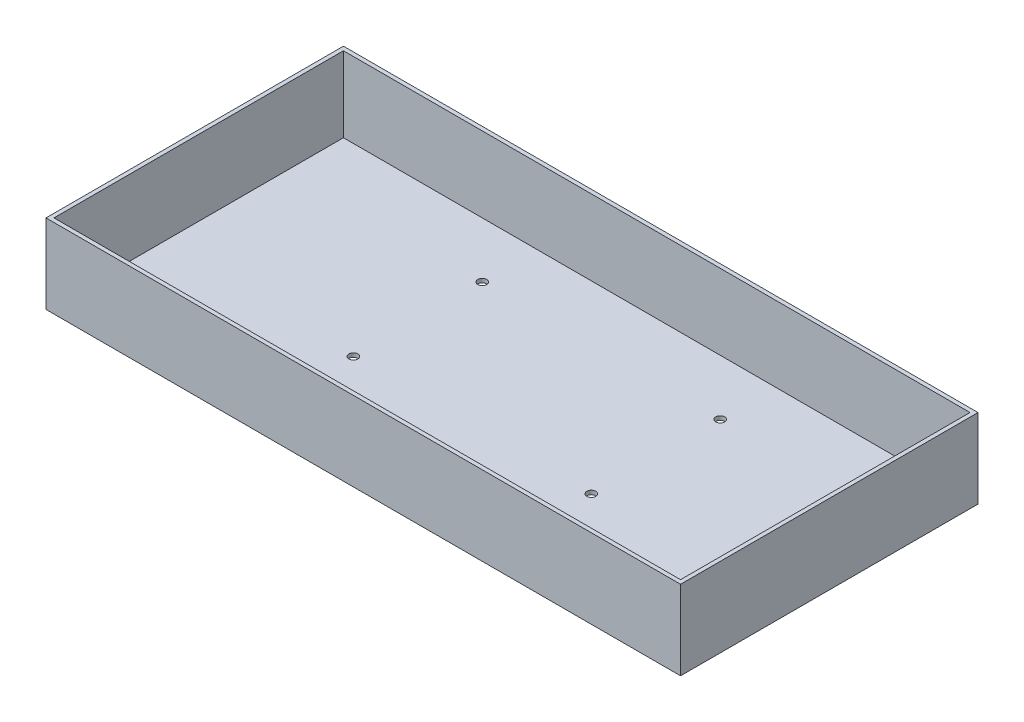
SolidWorks part; units mm, degrees
ref_plane "前视基准面" through (0, 0, 0) normal (0, 0, 1) x (1, 0, 0)
ref_plane "上视基准面" through (0, 0, 0) normal (0, 1, 0) x (1, 0, 0)
ref_plane "右视基准面" through (0, 0, 0) normal (1, 0, 0) x (0, 0, -1)
sketch "草图1" plane through (0, 0, 0) normal (0, 1, 0) x (1, 0, 0)
  line L1 (0, 0) -> (320, 0)
  line L2 (0, 0) -> (0, 150)
  line L3 (0, 150) -> (320, 150)
  line L4 (320, 0) -> (320, 150)
  dimension "D1" = 320
  dimension "D2" = 150
extrude "凸台-拉伸1" add sketch "草图1" along normal blind 40
shell "抽壳1" thickness 2
sketch "草图2" plane through (0, 0, 0) normal (0, -1, 0) x (-1, 0, 0)
  line L0 (-160, 120) -> (-160, 150) construction
  line L1 (-100, 55) -> (-220, 55) construction
  line L2 (-100, 55) -> (-100, 120) construction
  line L3 (-100, 120) -> (-220, 120) construction
  line L4 (-220, 55) -> (-220, 120) construction
  line L5 (-320, 150) -> (0, 150) construction
  circle A0 centre (-100, 55) radius 2.25
  circle A1 centre (-220, 55) radius 2.25
  circle A2 centre (-220, 120) radius 2.25
  circle A3 centre (-100, 120) radius 2.25
  dimension "D4" = 4.5
  dimension "D1" = 120
  dimension "D2" = 65
  dimension "D3" = 30
extrude "切除-拉伸1" cut sketch "草图2" against normal blind 2
